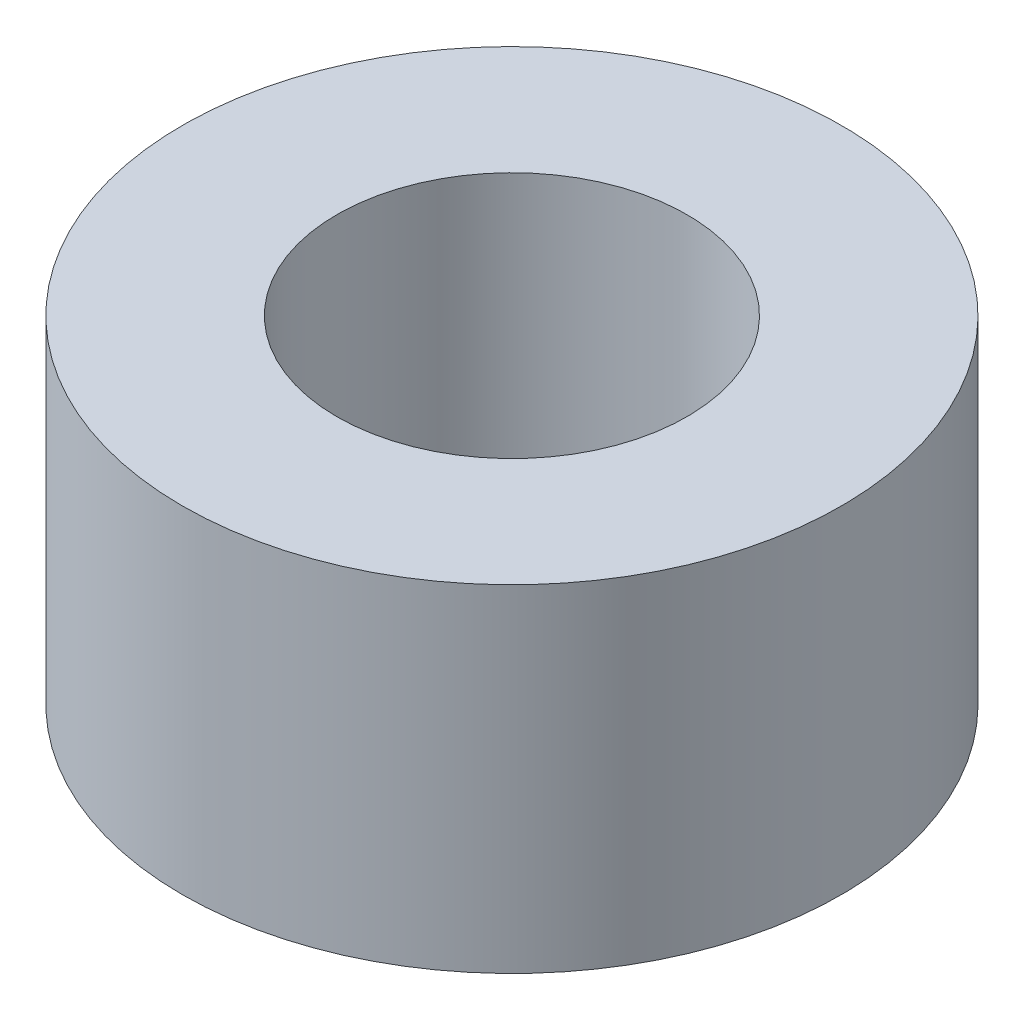
SolidWorks part; units mm, degrees
ref_plane "Front Plane" through (0, 0, 0) normal (0, 0, 1) x (1, 0, 0)
ref_plane "Top Plane" through (0, 0, 0) normal (0, 1, 0) x (1, 0, 0)
ref_plane "Right Plane" through (0, 0, 0) normal (1, 0, 0) x (0, 0, -1)
sketch "Sketch1" plane through (0, 0, 0) normal (0, 1, 0) x (1, 0, 0)
  circle A0 centre (0, 0) radius 4.8946
extrude "Boss-Extrude1" add sketch "Sketch1" along normal blind 5
sketch "Sketch2" plane through (0, 5, 0) normal (0, 1, 0) x (1, 0, 0)
  circle A0 centre (0, 0) radius 2.6
extrude "Cut-Extrude1" cut sketch "Sketch2" against normal through all
